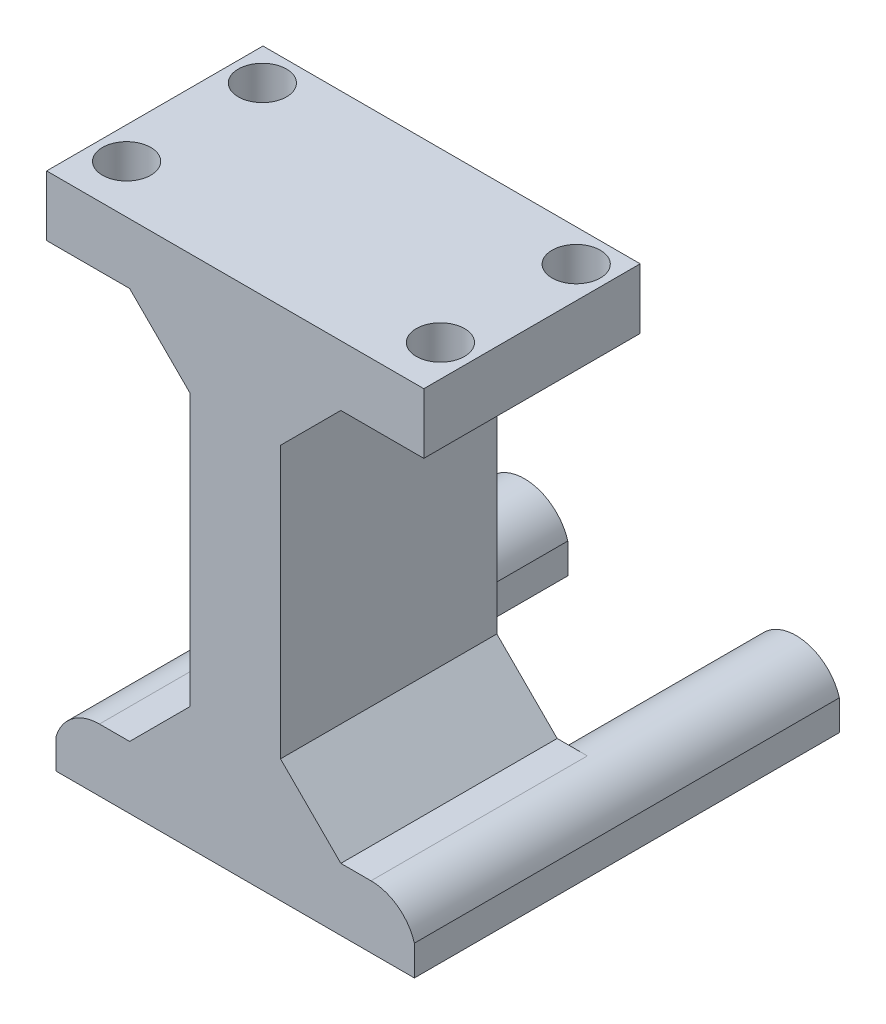
SolidWorks part; units mm, degrees
material "Acciaio in lega fuso"
ref_plane "Piano frontale" through (0, 0, 0) normal (0, 0, 1) x (1, 0, 0)
ref_plane "Piano superiore" through (0, 0, 0) normal (0, 1, 0) x (1, 0, 0)
ref_plane "Piano destro" through (0, 0, 0) normal (1, 0, 0) x (0, 0, -1)
sketch "Schizzo1" plane through (0, 0, 0) normal (0, 0, 1) x (1, 0, 0)
  line L0 (17.5, 0) -> (72.5, 0) construction
  line L3 (75.6253, 4.2857) -> (104.3747, 4.2857)
  line L4 (-15.1042, 4.2857) -> (14.3747, 4.2857)
  arc A0 (14.3747, 4.2857) -> (-14.3747, 4.2857) centre (0, 0) ccw
  arc A1 (104.3747, 4.2857) -> (75.6253, 4.2857) centre (90, 0) ccw
  dimension "D1" = 30
  dimension "D3" = 30
  dimension "D4" = 90
extrude "Estrusione-Estrusione1" add sketch "Schizzo1" against normal blind 105 contours L4 A0 | L3 A1
sketch "Schizzo2" plane through (0, 4.2857, 0) normal (0, -1, 0) x (1, 0, 0)
  line L1 (-14.3747, -105) -> (14.3747, -105)
  line L2 (-14.3747, -105) -> (-14.3747, 0)
  line L3 (-14.3747, 0) -> (14.3747, 0)
  line L4 (14.3747, -105) -> (14.3747, 0)
  line L5 (75.6253, -105) -> (104.3747, -105)
  line L6 (75.6253, -105) -> (75.6253, 0)
  line L7 (75.6253, 0) -> (104.3747, 0)
  line L8 (104.3747, -105) -> (104.3747, 0)
extrude "Estrusione-Estrusione2" add sketch "Schizzo2" along normal blind 10
sketch "Schizzo3" plane through (0, 0, 0) normal (0, 0, 1) x (1, 0, 0)
  line L1 (-14.3747, -5.7143) -> (104.3747, -5.7143)
  line L2 (-14.3747, -5.7143) -> (-14.3747, 4.2857)
  line L3 (0, 15) -> (90, 15)
  line L4 (104.3747, -5.7143) -> (104.3747, 4.2857)
  arc A0 (14.3747, 4.2857) -> (-14.3747, 4.2857) centre (0, 0) ccw construction
  arc A1 (0, 15) -> (-14.3747, 4.2857) centre (0, 0) ccw
  arc A2 (104.3747, 4.2857) -> (75.6253, 4.2857) centre (90, 0) ccw construction
  arc A3 (104.3747, 4.2857) -> (90, 15) centre (90, 0) ccw
extrude "Estrusione-Estrusione3" add sketch "Schizzo3" against normal mid plane 71.7
sketch "Schizzo4" plane through (0, 15, 0) normal (0, 1, 0) x (1, 0, 0)
  line L0 (90, -35.85) -> (0, -35.85) construction
  line L1 (30, -35.85) -> (60, -35.85)
  line L2 (30, -35.85) -> (30, 35.85)
  line L3 (30, 35.85) -> (60, 35.85)
  line L4 (60, -35.85) -> (60, 35.85)
  line L5 (90, 35.85) -> (0, 35.85) construction
  dimension "D1" = 30
  dimension "D2" = 30
extrude "Estrusione-Estrusione4" add sketch "Schizzo4" along normal blind 130
sketch "Schizzo5" plane through (0, 145, -145) normal (0, -1, 0) x (1, 0, 0)
  line L0 (107.5074, 180.85) -> (-17.5074, 109.15) construction
  line L1 (107.5074, 109.15) -> (-17.5074, 180.85) construction
  line L2 (25, 130) -> (65, 160) construction
  line L3 (65, 130) -> (25, 160) construction
  line L8 (-17.5074, 109.15) -> (107.5074, 109.15)
  line L9 (107.5074, 109.15) -> (107.5074, 180.85)
  line L10 (107.5074, 180.85) -> (-17.5074, 180.85)
  line L11 (-17.5074, 180.85) -> (-17.5074, 109.15)
  arc A8 (97, 156.85) -> (97, 172.85) centre (97, 164.85) ccw
  arc A9 (97, 172.85) -> (97, 156.85) centre (97, 164.85) ccw
  arc A10 (97, 127.85) -> (97, 111.85) centre (97, 119.85) ccw
  arc A11 (97, 111.85) -> (97, 127.85) centre (97, 119.85) ccw
  arc A12 (-7, 127.85) -> (-7, 111.85) centre (-7, 119.85) ccw
  arc A13 (-7, 111.85) -> (-7, 127.85) centre (-7, 119.85) ccw
  arc A14 (-7, 156.85) -> (-7, 172.85) centre (-7, 164.85) ccw
  arc A15 (-7, 172.85) -> (-7, 156.85) centre (-7, 164.85) ccw
  point P20 (45, 145)
  point P21 (45, 145)
  dimension "D1" = 8
  dimension "D2" = 8
  dimension "D7" = 8
  dimension "D8" = 8
  dimension "D12" = 8
  dimension "D13" = 8
  dimension "D17" = 8
  dimension "D18" = 8
  dimension "D3" = 16
  dimension "D4" = 10.5074
  dimension "D5" = 10.5074
  dimension "D6" = 10.7
  dimension "D9" = 71.7
  dimension "D10" = 125.0147
  dimension "D11" = 10.5074
  dimension "D14" = 10.7
  dimension "D15" = 16
  dimension "D16" = 10.5074
extrude "Estrusione-Estrusione5" add sketch "Schizzo5" against normal blind 20
chamfer "Smusso1" distance 20 angle 45 4 edges at (60, 145, 0) (30, 145, 0) (30, 15, 0) (60, 15, 0)
